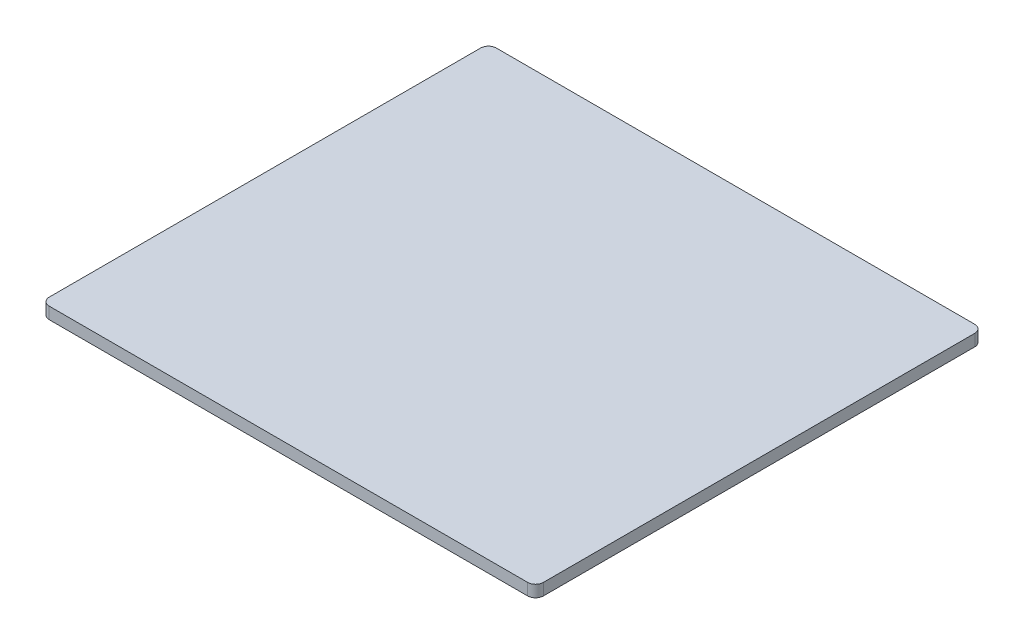
SolidWorks part; units mm, degrees
ref_plane "Front Plane" through (0, 0, 0) normal (0, 0, 1) x (1, 0, 0)
ref_plane "Top Plane" through (0, 0, 0) normal (0, 1, 0) x (1, 0, 0)
ref_plane "Right Plane" through (0, 0, 0) normal (1, 0, 0) x (0, 0, -1)
sketch "Sketch1" plane through (0, 0, 0) normal (0, 1, 0) x (1, 0, 0)
  line L1 (-7.505, 17.9653) -> (55.495, 17.9653)
  line L2 (-7.505, 17.9653) -> (-7.505, -39.0347)
  line L3 (-7.505, -39.0347) -> (55.495, -39.0347)
  line L4 (55.495, 17.9653) -> (55.495, -39.0347)
  dimension "D1" = 57
  dimension "D2" = 63
extrude "Boss-Extrude1" add sketch "Sketch1" along normal blind 1.5
fillet "Fillet1" radius 1 1 edges at (55.495, 0.75, 39.0347)
fillet "Fillet2" radius 1 1 edges at (55.495, 0.75, -17.9653)
fillet "Fillet3" radius 1 2 edges at (-7.505, 0.75, -17.9653) (-7.505, 0.75, 39.0347)
